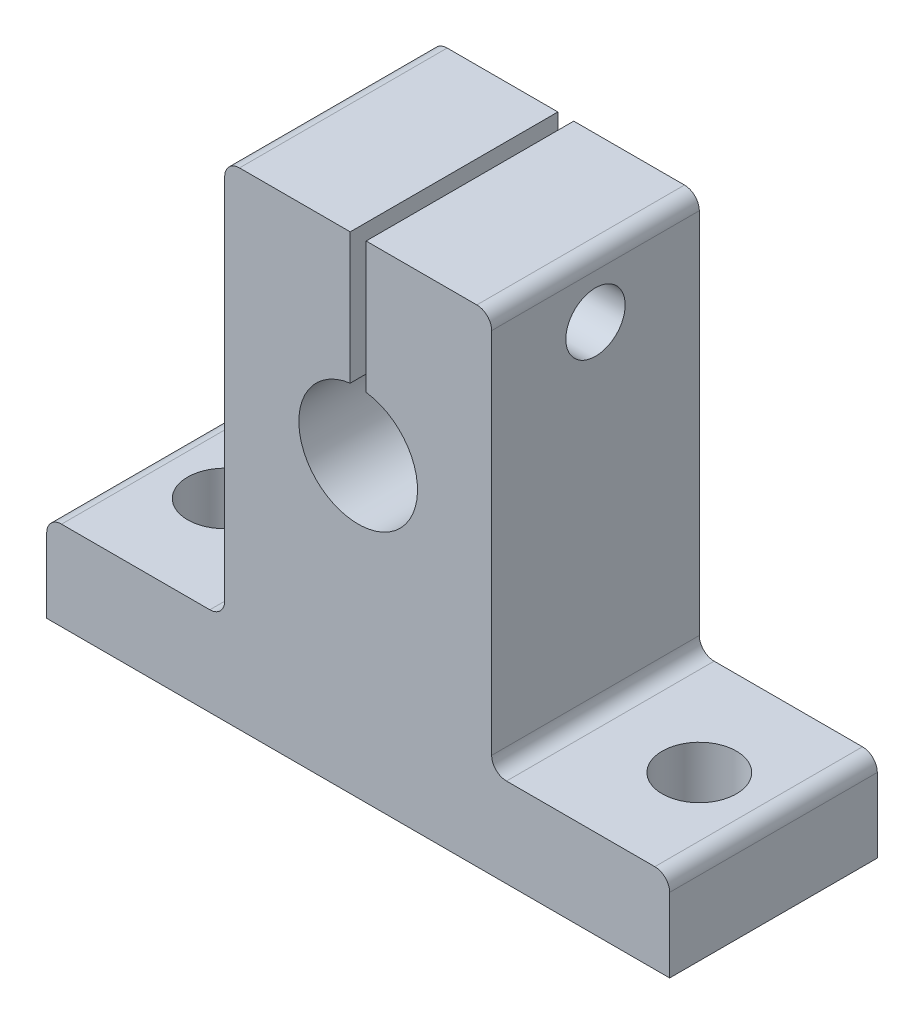
SolidWorks part; units mm, degrees
material "1.4057 (X17CrNi16-2)"
ref_plane "前视基准面" through (0, 0, 0) normal (0, 0, 1) x (1, 0, 0)
ref_plane "上视基准面" through (0, 0, 0) normal (0, 1, 0) x (1, 0, 0)
ref_plane "右视基准面" through (0, 0, 0) normal (1, 0, 0) x (0, 0, -1)
sketch "草图1" plane through (0, 0, 0) normal (0, 0, 1) x (1, 0, 0)
  line L0 (-22.7071, -12.2727) -> (19.2929, -12.2727)
  line L1 (19.2929, -12.2727) -> (19.2929, -6.2727)
  line L2 (19.2929, -6.2727) -> (7.2929, -6.2727)
  line L3 (7.2929, -6.2727) -> (7.2929, 20.5273)
  line L4 (7.2929, 20.5273) -> (0.9293, 20.5273)
  line L5 (-1.7071, 7.7273) -> (-1.7071, -3.7261)
  line L6 (-22.7071, -6.2727) -> (-10.7071, -6.2727)
  line L7 (-22.7071, -12.2727) -> (-22.7071, -6.2727)
  line L8 (-10.7071, -6.2727) -> (-10.7071, 20.5273)
  line L9 (-10.7071, 20.5273) -> (0.9293, 20.5273)
  circle A0 centre (-1.7071, 7.7273) radius 4
  point P13 (-1.7071, -12.2727)
  dimension "D5" = 8
  dimension "D1" = 20
  dimension "D2" = 21
  dimension "D3" = 9
  dimension "D4" = 32.8
  dimension "D6" = 6
extrude "凸台-拉伸1" add sketch "草图1" along normal blind 14
sketch "草图2" plane through (0, -6.2727, 0) normal (0, 1, 0) x (1, 0, 0)
  line L0 (-22.7071, -14) -> (-22.7071, 0) construction
  circle A0 centre (-17.7071, -7) radius 2.5
  circle A1 centre (14.2929, -7) radius 2.5
  dimension "D3" = 5
  dimension "D4" = 5
  dimension "D1" = 32
  dimension "D2" = 5
extrude "切除-拉伸1" cut sketch "草图2" against normal blind 14
sketch "草图3" plane through (0, 20.5273, 0) normal (0, 1, 0) x (1, 0, 0)
  line L1 (-10.7071, 0) -> (7.2929, 0) construction
  line L2 (-10.7071, -14) -> (7.2929, -14) construction
  line L3 (-2.2427, -14) -> (-1.1714, -14)
  line L4 (-1.1714, -14) -> (-1.1714, 0)
  line L5 (-1.1714, 0) -> (-2.2427, 0)
  line L6 (-2.2427, -14) -> (-2.2427, 0)
extrude "切除-拉伸2" cut sketch "草图3" against normal blind 14
sketch "草图4" plane through (7.2929, 0, 0) normal (1, 0, 0) x (0, 0, -1)
  line L0 (-14, 20.5273) -> (0, 20.5273) construction
  circle A0 centre (-7, 16.5273) radius 2
  dimension "D1" = 4
  dimension "D2" = 4
extrude "切除-拉伸3" cut sketch "草图4" against normal blind 60
fillet "圆角1" radius 1 4 edges at (7.2929, 20.5273, 7) (19.2929, -6.2727, 7) (-22.7071, -6.2727, 7) (-10.7071, 20.5273, 7)
fillet "圆角2" radius 1 2 edges at (-10.7071, -6.2727, 7) (7.2929, -6.2727, 7)
